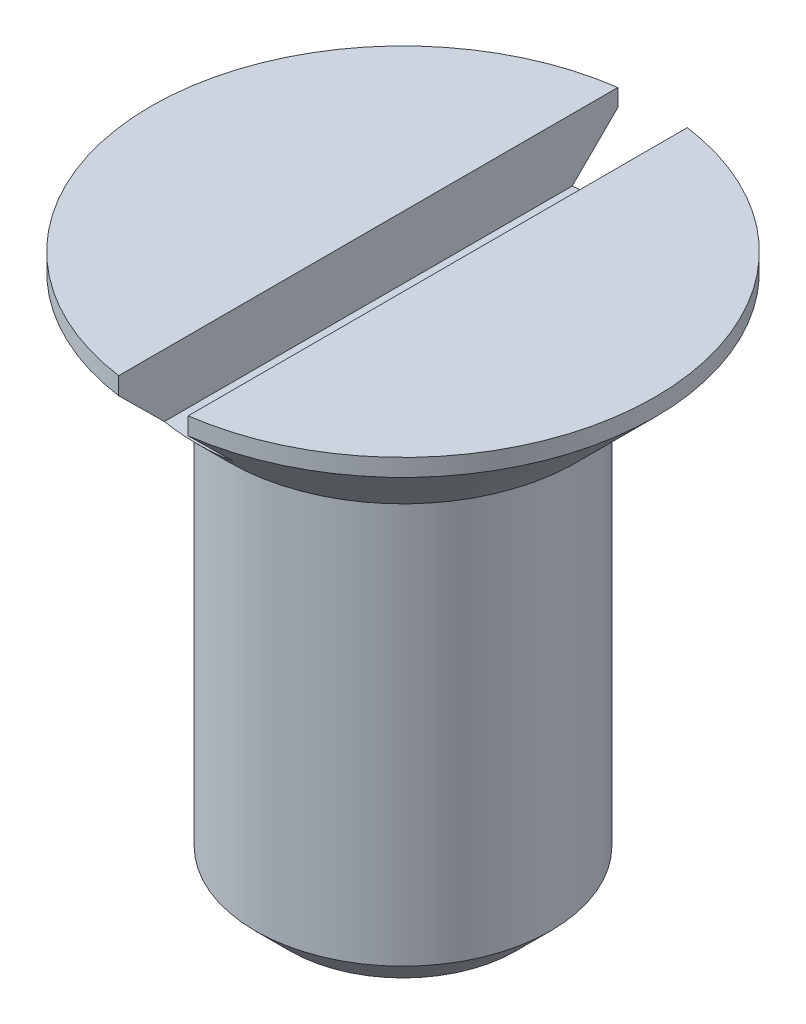
SolidWorks part; units mm, degrees
ref_plane "Alzado" through (0, 0, 0) normal (0, 0, 1) x (1, 0, 0)
ref_plane "Planta" through (0, 0, 0) normal (0, 1, 0) x (1, 0, 0)
ref_plane "Vista lateral" through (0, 0, 0) normal (1, 0, 0) x (0, 0, -1)
sketch "Sketch1" plane through (0, 0, 0) normal (0, 1, 0) x (1, 0, 0)
  circle A0 centre (0, 0) radius 0.725
  dimension "D1" = 1.45
extrude "Boss-Extrude1" add sketch "Sketch1" along normal blind 0.275
sketch "Sketch2" plane through (0, 0, 0) normal (0, 1, 0) x (1, 0, 0)
  circle A0 centre (0, 0) radius 0.425
  dimension "D1" = 0.85
extrude "Boss-Extrude2" add sketch "Sketch2" against normal blind 1.305
chamfer "Chamfer1" distance 0.1 angle 45 1 edges at (0, -1.305, 0.425)
chamfer "Chamfer2" distance 0.225 angle 45 1 edges at (0, 0, 0.725)
sketch "Sketch3" plane through (0, 0, 0) normal (0, 0, 1) x (1, 0, 0)
  line L0 (0, -1000) -> (0, 49000) construction
  line L1 (-0.1, -999.9755) -> (-0.1, 49000.0245) construction
  line L2 (0.725, 0.275) -> (-0.725, 0.275) construction
  line L3 (0.725, 0.275) -> (-0.725, 0.275) construction
  line L4 (-1000.5539, 0.095) -> (48999.4461, 0.095) construction
  line L5 (0.1, 0.6416) -> (-0.1, 0.6416)
  line L6 (-0.1, 0.6416) -> (-0.1, 0.095)
  line L7 (-0.1, 0.095) -> (0.1, 0.095)
  line L8 (0.1, 0.6416) -> (0.1, 0.095)
  point P14 (0, 0.095)
  point P15 (0, 0.6416)
  dimension "D1" = 0.18
  dimension "D2" = 0.1
extrude "Cut-Extrude1" cut sketch "Sketch3" against normal through all both and the other way through all
